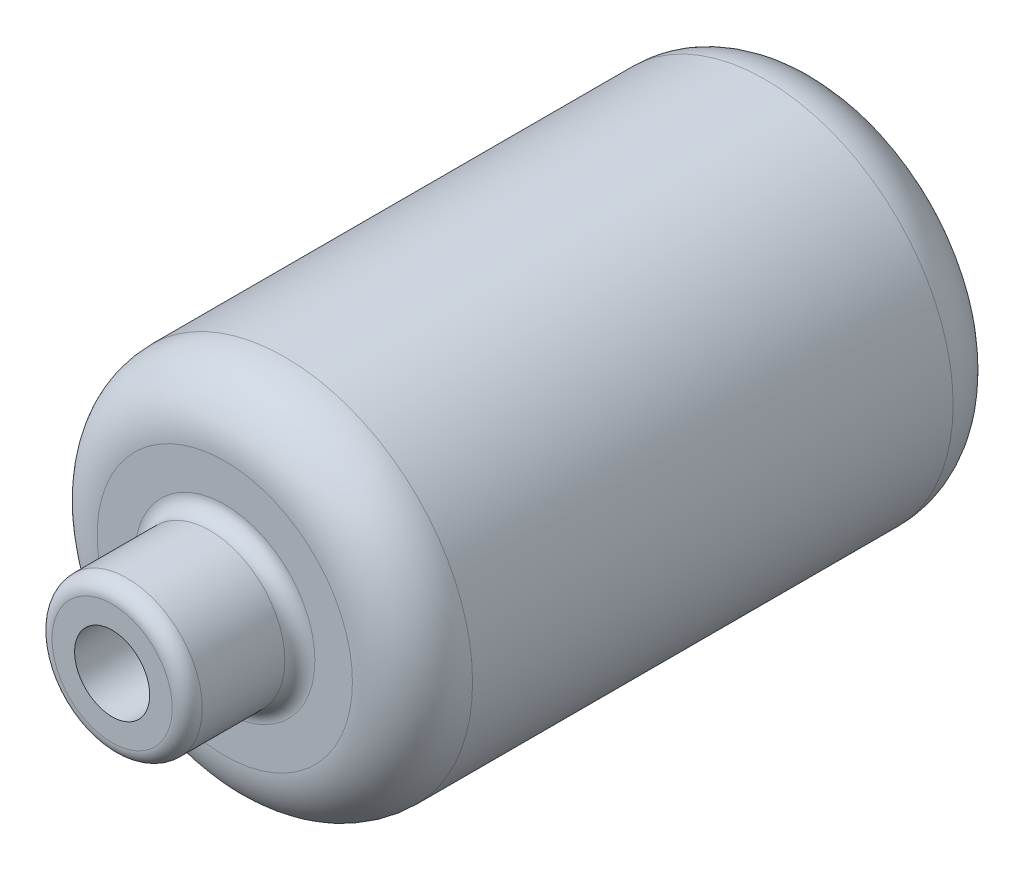
SolidWorks part; units mm, degrees
ref_plane "Front Plane" through (0, 0, 0) normal (0, 0, 1) x (1, 0, 0)
ref_plane "Top Plane" through (0, 0, 0) normal (0, 1, 0) x (1, 0, 0)
ref_plane "Right Plane" through (0, 0, 0) normal (1, 0, 0) x (0, 0, -1)
sketch "Sketch1" plane through (0, 0, 0) normal (0, 0, 1) x (1, 0, 0)
  circle A0 centre (0, 0) radius 25
  dimension "D1" = 50
extrude "Boss-Extrude1" add sketch "Sketch1" along normal blind 80
sketch "Sketch2" plane through (0, 0, 80) normal (0, 0, 1) x (1, 0, 0)
  circle A0 centre (0, 0) radius 10
  dimension "D1" = 20
extrude "Boss-Extrude2" add sketch "Sketch2" along normal blind 15
fillet "Fillet1" radius 8 1 edges at (25, 0, 80)
fillet "Fillet2" radius 8 1 edges at (25, 0, 0)
fillet "Fillet3" radius 2 2 edges at (10, 0, 80) (10, 0, 95)
sketch "Sketch3" plane through (0, 0, 95) normal (0, 0, 1) x (1, 0, 0)
  circle A0 centre (0, 0) radius 5
  dimension "D1" = 10
extrude "Cut-Extrude1" cut sketch "Sketch3" against normal blind 26
